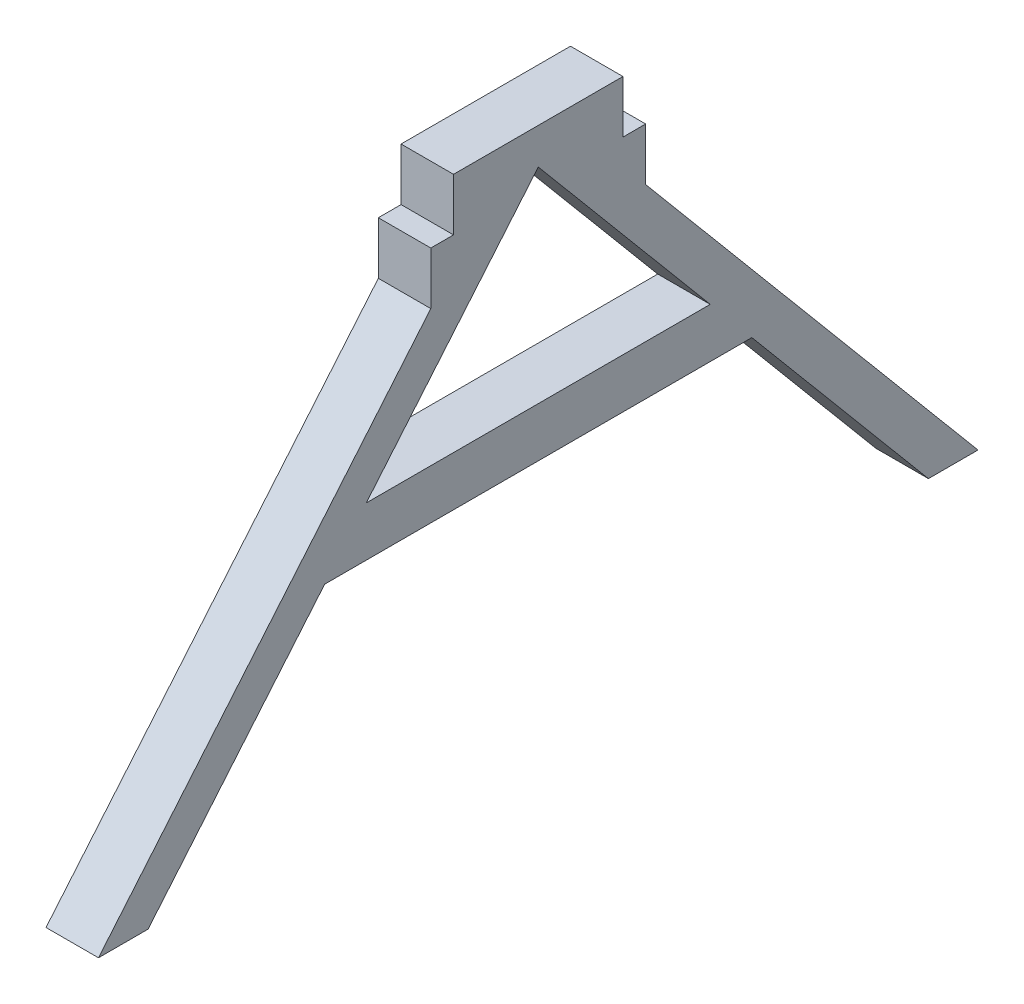
SolidWorks part; units mm, degrees
ref_plane "Front Plane" through (0, 0, 0) normal (0, 0, 1) x (1, 0, 0)
ref_plane "Top Plane" through (0, 0, 0) normal (0, 1, 0) x (1, 0, 0)
ref_plane "Right Plane" through (0, 0, 0) normal (1, 0, 0) x (0, 0, -1)
sketch "Sketch1" plane through (0, 0, 0) normal (1, 0, 0) x (0, 0, -1)
  line L13 (0.7275, -5.4962) -> (-19.3797, -29.4592)
  line L14 (-19.3797, -29.4592) -> (-16.3797, -29.4592)
  line L15 (-16.3797, -29.4592) -> (-5.6954, -16.7261)
  line L16 (7.2275, -1.3251) -> (17.6332, -13.7261)
  line L17 (30.8348, -29.4592) -> (33.8348, -29.4592)
  line L18 (33.8348, -29.4592) -> (13.7275, -5.4962)
  line L19 (-3.1781, -13.7261) -> (17.6332, -13.7261)
  line L20 (-5.6954, -16.7261) -> (20.1505, -16.7261)
  line L21 (20.1505, -16.7261) -> (30.8348, -29.4592)
  line L22 (-3.1781, -13.7261) -> (7.2275, -1.3251)
  line L23 (-3.1781, -13.7261) -> (-6.1781, -13.7261) construction
  line L24 (17.6332, -13.7261) -> (20.6332, -13.7261) construction
  line L25 (0.7275, -2.3212) -> (0.7275, -5.4962)
  line L26 (13.7275, -2.3212) -> (13.7275, -5.4962)
  line L27 (12.3525, -2.3212) -> (13.7275, -2.3212)
  line L28 (2.1025, -2.3212) -> (0.7275, -2.3212)
  line L29 (2.1025, -2.3212) -> (2.1025, 0.8538)
  line L30 (2.1025, 0.8538) -> (12.3525, 0.8538)
  line L31 (12.3525, 0.8538) -> (12.3525, -2.3212)
  dimension "D1" = 13
  dimension "D2" = 10.25
  dimension "D3" = 3.175
  dimension "D4" = 80
  dimension "D5" = 3.175
  dimension "D6" = 3
  dimension "D7" = 3
extrude "Boss-Extrude2" add sketch "Sketch1" along normal blind 3.175 contours L22 L16 L19
